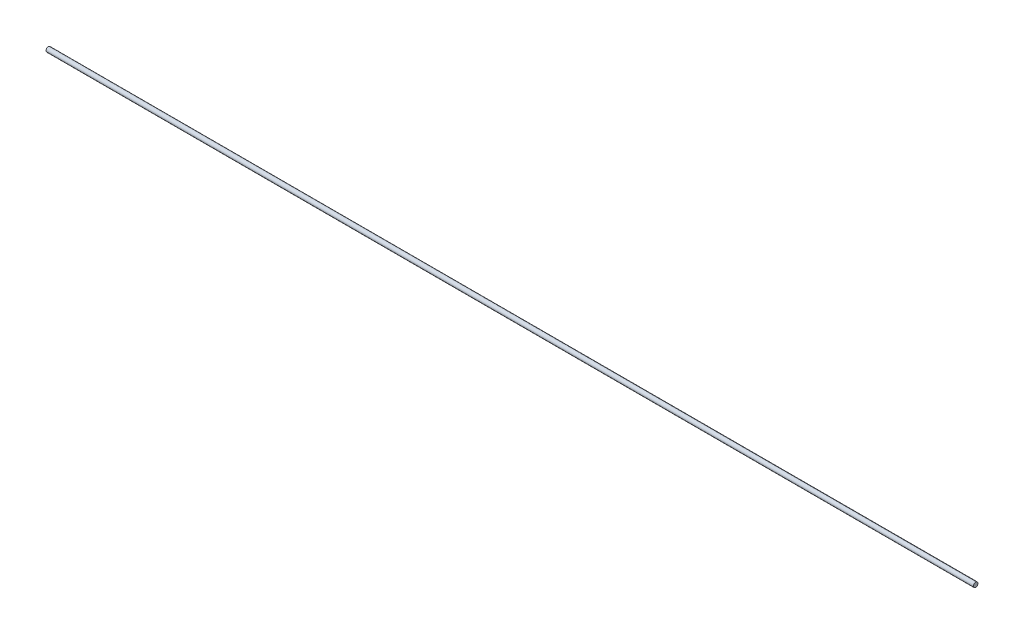
SolidWorks part; units mm, degrees
ref_plane "Front Plane" through (0, 0, 0) normal (0, 0, 1) x (1, 0, 0)
ref_plane "Top Plane" through (0, 0, 0) normal (0, 1, 0) x (1, 0, 0)
ref_plane "Right Plane" through (0, 0, 0) normal (1, 0, 0) x (0, 0, -1)
sketch "Sketch1" plane through (0, 0, 0) normal (1, 0, 0) x (0, 0, -1)
  circle A0 centre (0, 0) radius 2.5
  dimension "D1" = 5
extrude "Boss-Extrude1" add sketch "Sketch1" along normal blind 1000
